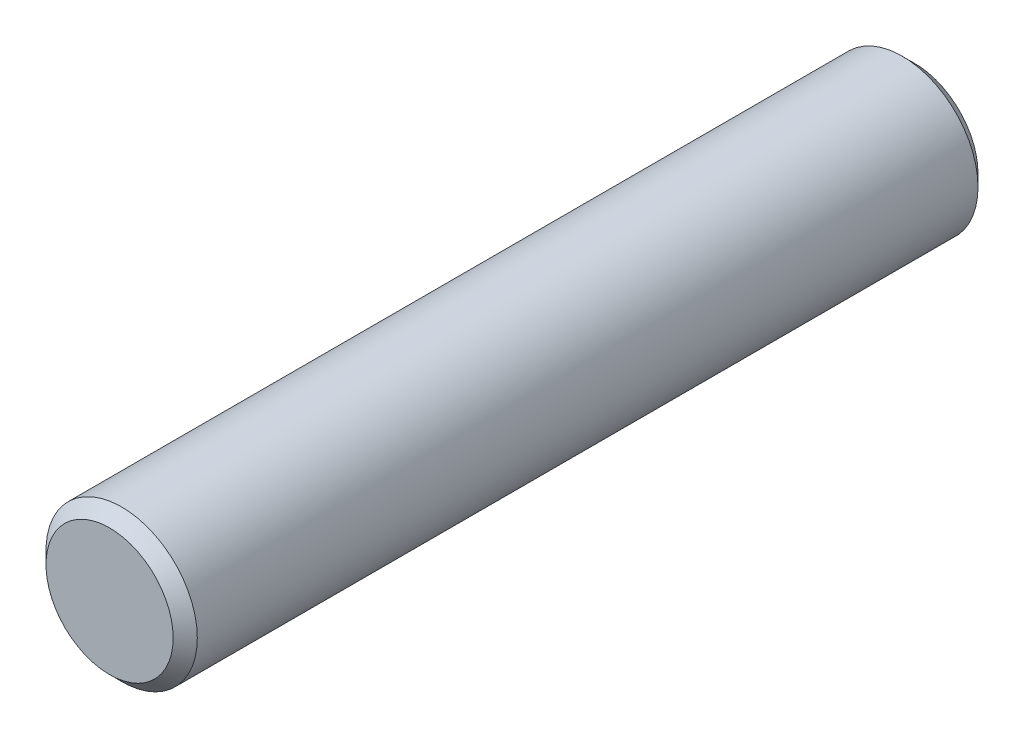
SolidWorks part; units mm, degrees
material "AISI 304"
ref_plane "Front Plane" through (0, 0, 0) normal (0, 0, 1) x (1, 0, 0)
ref_plane "Top Plane" through (0, 0, 0) normal (0, 1, 0) x (1, 0, 0)
ref_plane "Right Plane" through (0, 0, 0) normal (1, 0, 0) x (0, 0, -1)
sketch "Sketch1" plane through (0, 0, 0) normal (0, 0, 1) x (1, 0, 0)
  circle A0 centre (0, 0) radius 2.3876
  dimension "D1" = 4.7752
extrude "Extrude1" add sketch "Sketch1" along normal mid plane 25.4
chamfer "Chamfer1" distance 0.381 angle 45 2 edges at (2.3876, 0, -12.7) (2.3876, 0, 12.7)
